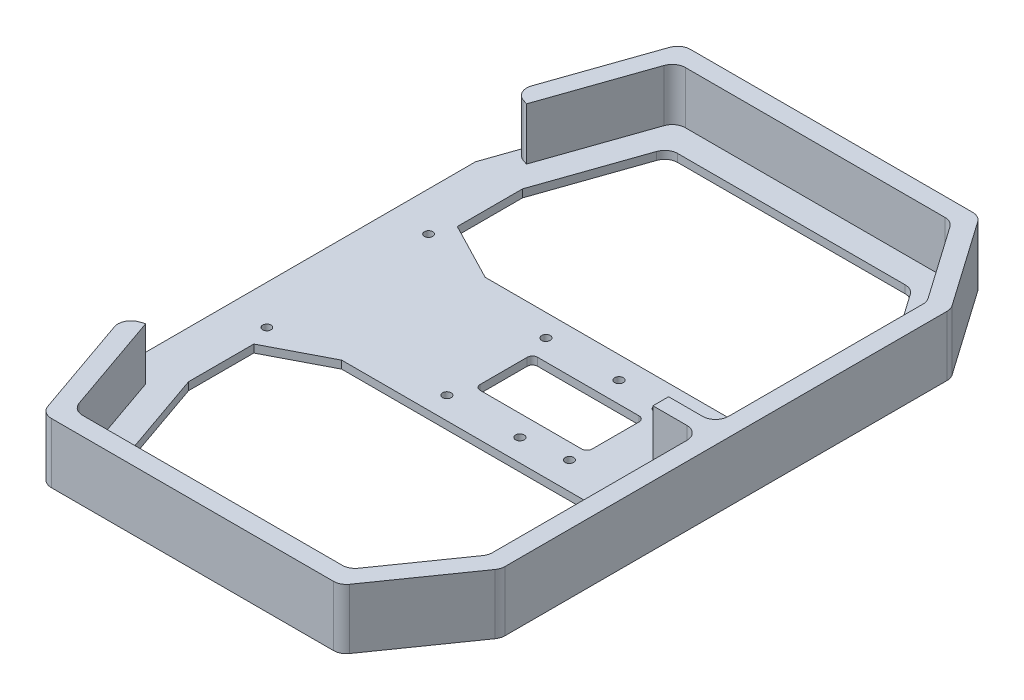
SolidWorks part; units mm, degrees
ref_plane "Front Plane" through (0, 0, 0) normal (0, 0, 1) x (1, 0, 0)
ref_plane "Top Plane" through (0, 0, 0) normal (0, 1, 0) x (1, 0, 0)
ref_plane "Right Plane" through (0, 0, 0) normal (1, 0, 0) x (0, 0, -1)
sketch "Sketch1" plane through (0, 0, 0) normal (0, 1, 0) x (1, 0, 0)
  line L0 (0, 0) -> (59180.0483, 0) construction
  line L1 (0, 0) -> (0, 59180.0483) construction
  line L2 (-15, -39) -> (-15, 39)
  line L5 (25.198, 27.5) -> (128, 27.5)
  line L6 (128, 27.5) -> (128, 80.9254)
  line L7 (110.7927, 105.5) -> (17.4422, 105.5)
  line L17 (25.198, -27.5) -> (128, -27.5)
  line L20 (5.3583, 122.5) -> (-15, 64)
  line L21 (-15, 64) -> (-15, 39)
  line L22 (3, 39) -> (3, 64)
  line L23 (3, 64) -> (17.4422, 105.5)
  line L24 (3, 39) -> (25.198, 27.5)
  line L26 (3, -39) -> (25.198, -27.5)
  line L27 (3, -39) -> (3, -64)
  line L28 (3, -64) -> (17.4422, -105.5)
  line L31 (5.3583, -122.5) -> (-15, -64)
  line L32 (-15, -39) -> (-15, -64)
  line L33 (-15, 64) -> (3, 64) construction
  line L34 (110.7927, 105.5) -> (128, 80.9254)
  line L35 (5.3583, 122.5) -> (119.6423, 122.5)
  line L36 (119.6423, 122.5) -> (145, 86.2855)
  line L37 (145, 86.2855) -> (145, -86.2855)
  line L38 (128, -27.5) -> (128, -80.9254)
  line L39 (119.6423, -122.5) -> (145, -86.2855)
  line L40 (110.7927, -105.5) -> (128, -80.9254)
  line L41 (110.7927, -105.5) -> (17.4422, -105.5)
  line L42 (5.3583, -122.5) -> (119.6423, -122.5)
  circle A0 centre (0, 31) radius 1.6
  circle A1 centre (0, -31) radius 1.6
  point P20 (145, 0)
  point P21 (140, 0)
  point P29 (-15, 0)
  dimension "D1" = 3.2
  dimension "D2" = 62
  dimension "D3" = 78
  dimension "D4" = 15
  dimension "D9" = 55
  dimension "D5" = 25
  dimension "D8" = 25
  dimension "D11" = 78
  dimension "D12" = 125
  dimension "D13" = 18
  dimension "D14" = 25
  dimension "D6" = 17
  dimension "D7" = 17
  dimension "D10" = 17
  dimension "D15" = 17
  dimension "D16" = 30
  dimension "D17" = 125
extrude "Boss-Extrude1" add sketch "Sketch1" along normal mid plane 3
sketch "Sketch2" plane through (0, 1.5, 0) normal (0, 1, 0) x (1, 0, 0)
  line L0 (0, 0) -> (50000, 0) construction
  line L1 (102.7, 11) -> (102.7, -11)
  line L2 (102.7, -11) -> (59.8, -11)
  line L3 (59.8, -11) -> (59.8, 11)
  line L4 (59.8, 11) -> (102.7, 11)
  circle A0 centre (57, 19) radius 1.65
  circle A1 centre (85, 19) radius 1.65
  circle A2 centre (102, 17) radius 1.65
  circle A3 centre (102, -17) radius 1.65
  circle A4 centre (85, -19) radius 1.65
  circle A5 centre (57, -19) radius 1.65
  dimension "D1" = 3.3
  dimension "D2" = 3.3
  dimension "D3" = 3.3
sketch "Sketch3" plane through (0, 1.5, 0) normal (0, 1, 0) x (1, 0, 0)
  line L0 (120, -3) -> (120, 3)
  line L1 (-200000, 0) -> (250000, 0) construction
  line L2 (120, 3) -> (138, 3)
  line L3 (138, 3) -> (138, 84.0784)
  line L4 (138, 84.0784) -> (115.9984, 115.5)
  line L5 (115.9984, 115.5) -> (10.334, 115.5)
  line L6 (10.334, 115.5) -> (-4.4642, 72.9771)
  line L7 (-4.4642, 72.9771) -> (-11.0753, 75.2778)
  line L8 (5.3583, 122.5) -> (-15, 64) construction
  line L9 (-11.0753, 75.2778) -> (5.3583, 122.5)
  line L10 (5.3583, 122.5) -> (119.6423, 122.5)
  line L11 (119.6423, 122.5) -> (145, 86.2855)
  line L12 (145, 86.2855) -> (145, -86.2855)
  line L13 (145, -86.2855) -> (145, 86.2855) construction
  line L14 (0, 0) -> (50000, 0) construction
  line L15 (119.6423, -122.5) -> (145, -86.2855)
  line L16 (5.3583, -122.5) -> (119.6423, -122.5)
  line L17 (-11.0753, -75.2778) -> (5.3583, -122.5)
  line L18 (-4.4642, -72.9771) -> (-11.0753, -75.2778)
  line L19 (10.334, -115.5) -> (-4.4642, -72.9771)
  line L20 (115.9984, -115.5) -> (10.334, -115.5)
  line L21 (138, -84.0784) -> (115.9984, -115.5)
  line L22 (138, -3) -> (138, -84.0784)
  line L23 (120, -3) -> (138, -3)
  point P25 (145, 0)
  point P34 (120, 0)
  dimension "D1" = 6
  dimension "D2" = 25
  dimension "D3" = 7
  dimension "D4" = 7
  dimension "D5" = 7
  dimension "D6" = 7
  dimension "D7" = 50
extrude "Boss-Extrude2" add sketch "Sketch3" along normal blind 20
fillet "Fillet1" radius 5 19 edges at (-11.0753, 11.5, 75.2778) (119.6423, 10, -122.5) (145, 10, -86.2855) (145, 10, 86.2855) (119.6423, 10, 122.5) (5.3583, 10, 122.5) (5.3583, 10, -122.5) (-11.0753, 11.5, -75.2778) (10.334, 11.5, 115.5) (115.9984, 11.5, 115.5) (138, 11.5, 84.0784) (138, 11.5, 3) (138, 11.5, -3) (17.4422, 0, -105.5) (128, 0, -80.9254) (110.7927, 0, -105.5) (138, 11.5, -84.0784) (115.9984, 11.5, -115.5) (10.334, 11.5, -115.5)
extrude "Cut-Extrude1" cut sketch "Sketch2" against normal through all
fillet "Fillet2" radius 2 4 edges at (102.7, 0, 11) (59.8, 0, 11) (102.7, 0, -11) (59.8, 0, -11)
equation "\"D8@Sketch1\"=\"D5@Sketch1\""
equation "\"D2@Sketch2\"=\"D1@Sketch2\""
equation "\"D3@Sketch2\"=\"D1@Sketch2\""
